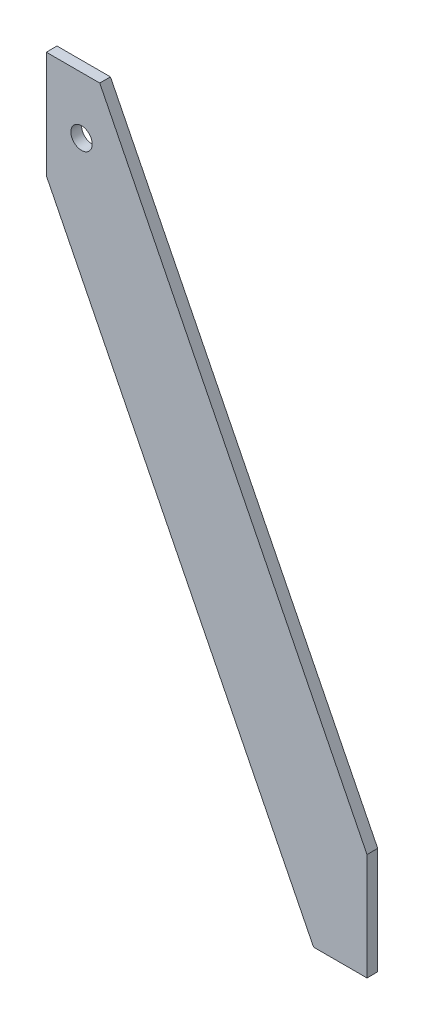
SolidWorks part; units mm, degrees
ref_plane "Front Plane" through (0, 0, 0) normal (0, 0, 1) x (1, 0, 0)
ref_plane "Top Plane" through (0, 0, 0) normal (0, 1, 0) x (1, 0, 0)
ref_plane "Right Plane" through (0, 0, 0) normal (1, 0, 0) x (0, 0, -1)
sketch "Sketch1" plane through (0, 0, 0) normal (0, 0, 1) x (1, 0, 0)
  line L0 (0, -83.3244) -> (0, -43.3244)
  line L1 (0, -83.3244) -> (0, 156.6756) construction
  line L2 (0, -83.3244) -> (-120, -83.3244) construction
  line L3 (-120, 156.6756) -> (-120, 116.6756)
  line L4 (-120, 156.6756) -> (-100, 156.6756)
  line L5 (0, -83.3244) -> (-20, -83.3244)
  line L6 (-100, 156.6756) -> (0, -43.3244)
  line L7 (-120, 116.6756) -> (-20, -83.3244)
  circle A0 centre (-106.8097, 135.4424) radius 4
  dimension "D1" = 240
  dimension "D2" = 40
  dimension "D3" = 120
extrude "Boss-Extrude1" add sketch "Sketch1" along normal blind 4
